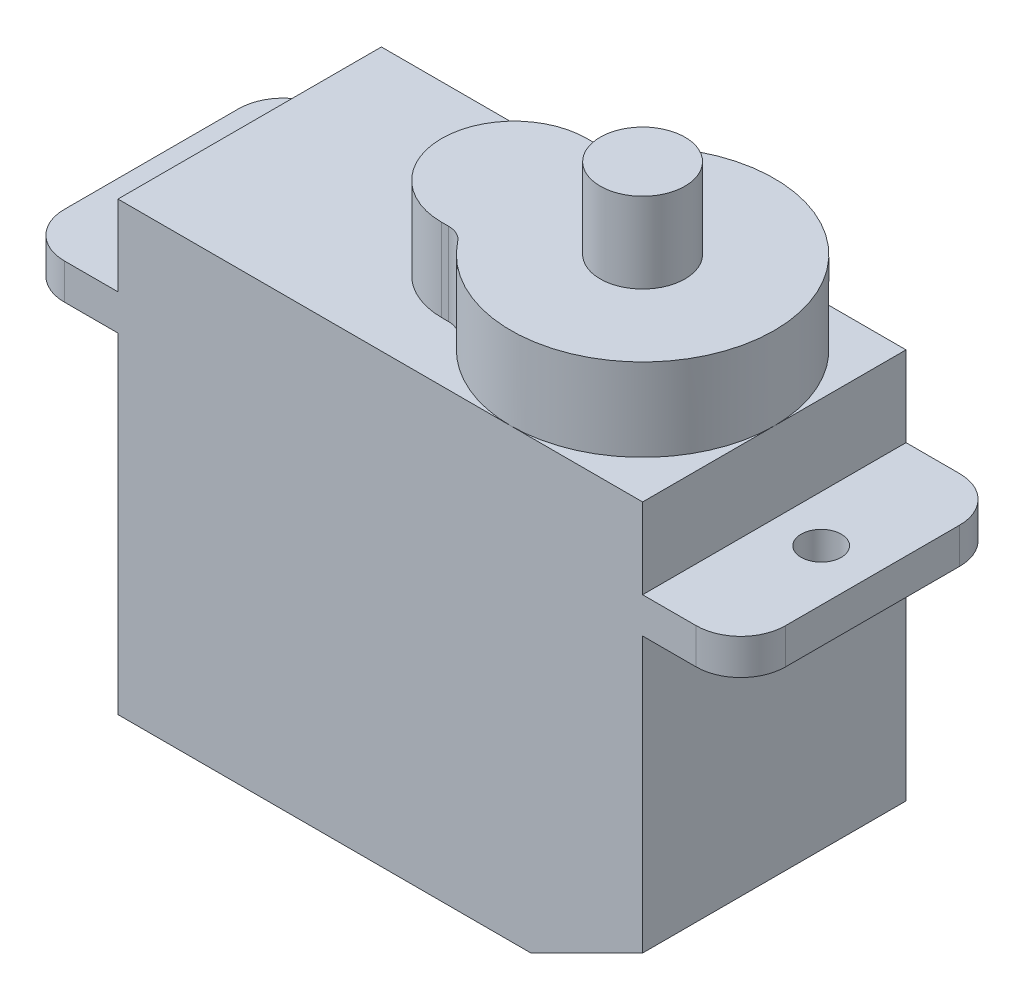
SolidWorks part; units mm, degrees
ref_plane "Płaszczyzna przednia" through (0, 0, 0) normal (0, 0, 1) x (1, 0, 0)
ref_plane "Płaszczyzna górna" through (0, 0, 0) normal (0, 1, 0) x (1, 0, 0)
ref_plane "Płaszczyzna prawa" through (0, 0, 0) normal (1, 0, 0) x (0, 0, -1)
sketch "Szkic1" plane through (0, 0, 0) normal (0, 0, 1) x (1, 0, 0)
  line L0 (0, 0) -> (0, 14.8)
  line L1 (0, 14.8) -> (-4.4, 14.8)
  line L2 (-4.4, 14.8) -> (-4.4, 16.4)
  line L3 (-4.4, 16.4) -> (0, 16.4)
  line L4 (0, 16.4) -> (0, 20)
  line L5 (0, 20) -> (23.5, 20)
  line L6 (23.5, 20) -> (23.5, 16.4)
  line L7 (23.5, 16.4) -> (27.9, 16.4)
  line L8 (27.9, 16.4) -> (27.9, 14.8)
  line L9 (27.9, 14.8) -> (23.5, 14.8)
  line L10 (23.5, 14.8) -> (23.5, 2.5)
  line L11 (23.5, 2.5) -> (18.5, 0)
  line L12 (18.5, 0) -> (0, 0)
  dimension "D1" = 14.8
  dimension "D2" = 1.6
  dimension "D3" = 20
  dimension "D4" = 4.4
  dimension "D5" = 23.5
  dimension "D6" = 5
  dimension "D7" = 2.5
extrude "Dodanie-wyciągnięcie1" add sketch "Szkic1" along normal blind 11.8 contours L4 L5 L6 L7 L8 L9 L10 L11 L12 L0 L1 L2 L3
sketch "Szkic2" plane through (0, 16.4, 0) normal (0, 1, 0) x (1, 0, 0)
  line L0 (-4.4, -5.9) -> (27.9, -5.9) construction
  line L1 (-4.4, -11.8) -> (-4.4, 0) construction
  line L2 (27.9, -11.8) -> (27.9, 0) construction
  circle A0 centre (-2.1, -5.9) radius 0.9
  circle A1 centre (25.6, -5.9) radius 0.9
  dimension "D1" = 1.8
  dimension "D2" = 1.8
  dimension "D3" = 2.3
  dimension "D4" = 2.3
extrude "Wytnij-wyciągnięcie1" cut sketch "Szkic2" against normal blind 11.8
fillet "Zaokrąglenie1" radius 2 4 edges at (27.9, 15.6, 11.8) (27.9, 15.6, 0) (-4.4, 15.6, 11.8) (-4.4, 15.6, 0)
sketch "Szkic3" plane through (0, 20, 0) normal (0, 1, 0) x (1, 0, 0)
  line L0 (0, -5.9) -> (23.5, -5.9) construction
  line L1 (0, -11.8) -> (0, 0) construction
  line L2 (23.5, -11.8) -> (23.5, 0) construction
  line L3 (0, 0) -> (23.5, 0) construction
  line L4 (23.5, -11.8) -> (23.5, 0) construction
  line L5 (11.85, -2.65) -> (12.1642, -2.65)
  line L6 (11.85, -9.15) -> (12.1642, -9.15)
  arc A0 (12.952, -9.5341) -> (12.952, -2.2659) centre (17.6, -5.9) ccw
  arc A1 (11.85, -2.65) -> (11.85, -9.15) centre (11.85, -5.9) ccw
  arc A2 (12.952, -9.5341) -> (12.1642, -9.15) centre (12.1642, -10.15) ccw
  arc A3 (12.952, -2.2659) -> (12.1642, -2.65) centre (12.1642, -1.65) cw
  dimension "D1" = 6.5
  dimension "D3" = 1
  dimension "D2" = 11.65
extrude "Dodanie-wyciągnięcie2" add sketch "Szkic3" along normal blind 3.7
sketch "Szkic4" plane through (0, 23.7, 0) normal (0, 1, 0) x (1, 0, 0)
  circle A0 centre (17.6, -5.9) radius 1.9
  dimension "D1" = 3.8
extrude "Dodanie-wyciągnięcie3" add sketch "Szkic4" along normal blind 3.6
